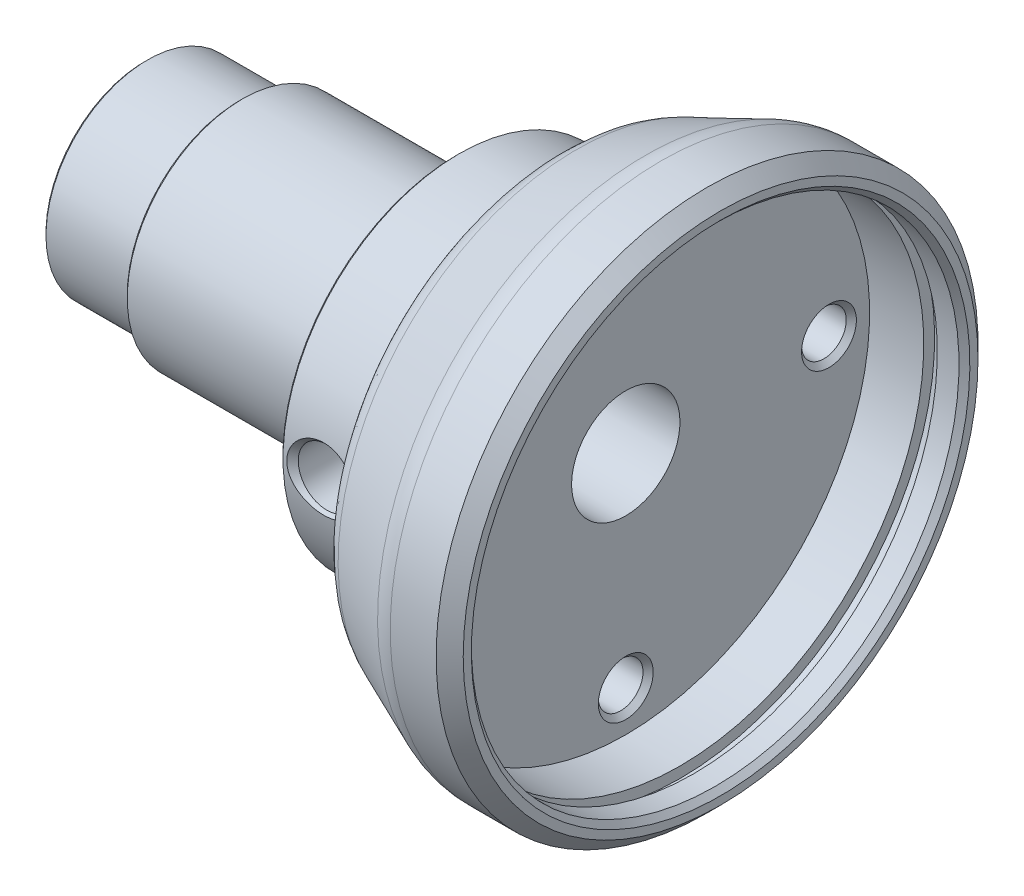
SolidWorks part; units mm, degrees
material "7075-T6 (SN)"
ref_plane "Ebene vorne" through (0, 0, 0) normal (0, 0, 1) x (1, 0, 0)
ref_plane "Ebene oben" through (0, 0, 0) normal (0, 1, 0) x (1, 0, 0)
ref_plane "Ebene rechts" through (0, 0, 0) normal (1, 0, 0) x (0, 0, -1)
sketch "Skizze1" plane through (0, 0, 0) normal (0, 0, 1) x (1, 0, 0)
  line L0 (7.2, -8.5) -> (22, -8.5)
  line L1 (30.5, -17.0287) -> (29.5, -13)
  line L2 (36.9382, -19.7615) -> (30.5, -17.0287)
  line L3 (7, -7.5) -> (7, -8.3)
  line L4 (7, -7.5) -> (0.2, -7.5)
  line L5 (0, -7.3) -> (0, -4.2)
  line L6 (23, -9.5) -> (23, -12.8)
  line L7 (23.2, -13) -> (29.5, -13)
  line L8 (38.1104, -20) -> (42.5, -20)
  line L9 (23, -12.8) -> (23.2, -13)
  line L10 (-24.3468, 0) -> (45.2859, 0)
  line L11 (42.5, -20) -> (42.5, -18)
  line L12 (42.5, -18) -> (40.5, -18)
  line L13 (7, -8.3) -> (7.2, -8.5)
  line L14 (0.2, -7.5) -> (0, -7.3)
  line L15 (0.2, -4) -> (0, -4.2)
  line L17 (35.5, -4) -> (0.2, -4)
  line L18 (35.5, -18) -> (35.5, -4)
  line L19 (40.5, -18) -> (40.5, -18.8)
  line L20 (40.5, -18.8) -> (39.5, -18.8)
  line L21 (39.5, -18.8) -> (39.5, -18)
  line L22 (39.5, -18) -> (35.5, -18)
  arc A0 (38.1104, -20) -> (36.9382, -19.7615) centre (38.1104, -17) cw
  arc A2 (22, -8.5) -> (23, -9.5) centre (22, -9.5) cw
  point P4 (7, -8.5)
  point P6 (0, -7.5)
  point P8 (0, -4)
  point P15 (23, -13)
  point P20 (27.6845, 39.9684)
  point P26 (37.5, -20)
  dimension "D23" = 3
  dimension "D5" = 13
  dimension "D13" = 1
  dimension "D14" = 0
  dimension "D2" = 7
  dimension "D3" = 18
  dimension "D4" = 23
  dimension "D6" = 4
  dimension "D7" = 12
  dimension "D8" = 35.5
  dimension "D9" = 23
  dimension "D10" = 7
  dimension "D11" = 8.5
  dimension "D12" = 7.5
  dimension "D15" = 0
  dimension "D16" = 9
  dimension "D17" = 2
  dimension "D18" = 1
  dimension "D19" = 0.8
  dimension "D20" = 2
  dimension "D22" = 5
  dimension "D26" = 42.5
revolve "Rotation1" add sketch "Skizze1" angle 360 about L10
chamfer "Fase6" distance 1 angle 45 1 edges at (42.5, -20, 0)
chamfer "Fase7" distance 0.4 angle 45 1 edges at (42.5, -18, 0)
fillet "Verrundung1" radius 3 1 edges at (30.5, -17.0287, 0)
fillet "Verrundung2" radius 1 1 edges at (29.5, -13, 0)
sketch "Skizze2" plane through (35.5, 0, 0) normal (1, 0, 0) x (0, 0, -1)
  circle A0 centre (0, 0) radius 15
  point P3 (0, 15)
  point P4 (15, 0)
  point P5 (0, -15)
  point P6 (-15, 0)
  dimension "D1" = 30
hole_wizard "M4 Gewindebohrung1" positions "3D-Skizze1" profile "Skizze3" tap size "M4" standard "DIN"
sketch3d "3D-Skizze1"
  point P0 (35.5, 15, 0)
  point P3 (35.5, 0, 15)
  point P6 (35.5, -15, 0)
  point P9 (35.5, 0, -15)
sketch "Skizze3" plane through (35.5, 15, 0) normal (0, 1, 0) x (0, 0, -1)
  line L0 (0, 0) -> (0, 12.4914)
  line L1 (0, 12.4914) -> (1.65, 11.5)
  line L2 (1.65, 11.5) -> (1.65, 0.375)
  line L3 (1.65, 0.375) -> (2.025, 0)
  line L5 (2.025, 0) -> (0, 0)
  line L6 (-1.65, 0.375) -> (-2.025, 0) construction
  line L10 (0, 12.4914) -> (-1.65, 11.5) construction
  line L11 (0, -6.35) -> (0, 107.95) construction
  dimension "Bohrerdurchmesser" = 3.3
  dimension "Bohrungstiefe" = 11.5
  dimension "Senkdurchmesser (Oben)" = 4.05
  dimension "Senkwinkel (Oben)" = 90
  dimension "Spitzenwinkel" = 118
ref_plane "Ebene3" through (0, 0, 13) normal (0, 0, 1) x (1, 0, 0)
sketch "Skizze29" plane through (0, 0, 13) normal (0, 0, 1) x (1, 0, 0)
  line L0 (23, 12.8) -> (23, -12.8) construction
  line L1 (0, 0) -> (26, 0) construction
  point P0 (26, 0)
  dimension "D1" = 3
hole_wizard "M5 Gewindebohrung2" positions "Skizze31" profile "Skizze30" tap size "M5" standard "DIN"
sketch "Skizze31" plane through (0, 0, 13) normal (0, 0, 1) x (1, 0, 0)
  point P1 (26, 0)
sketch "Skizze30" plane through (26, 0, 13) normal (1, 0, 0) x (0, -1, 0)
  line L0 (0, 0) -> (0, 15.2618)
  line L1 (0, 15.2618) -> (2.1, 14)
  line L2 (2.1, 14) -> (2.1, 0.425)
  line L3 (2.1, 0.425) -> (2.525, 0)
  line L5 (2.525, 0) -> (0, 0)
  line L6 (-2.1, 0.425) -> (-2.525, 0) construction
  line L10 (0, 15.2618) -> (-2.1, 14) construction
  line L11 (0, -6.35) -> (0, 107.95) construction
  dimension "Bohrerdurchmesser" = 4.2
  dimension "Bohrungstiefe" = 14
  dimension "Senkdurchmesser (Oben)" = 5.05
  dimension "Senkwinkel (Oben)" = 90
  dimension "Spitzenwinkel" = 118
